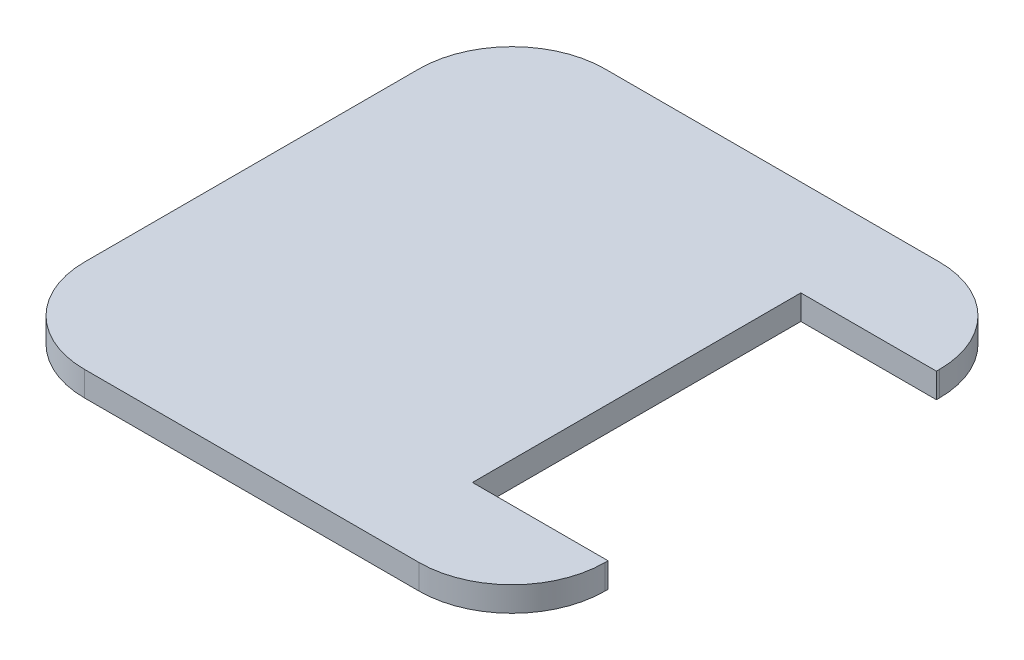
SolidWorks part; units mm, degrees
ref_plane "Front Plane" through (0, 0, 0) normal (0, 0, 1) x (1, 0, 0)
ref_plane "Top Plane" through (0, 0, 0) normal (0, 1, 0) x (1, 0, 0)
ref_plane "Right Plane" through (0, 0, 0) normal (1, 0, 0) x (0, 0, -1)
sketch "Layer1" plane through (0, 0, 0) normal (0, 1, 0) x (1, 0, 0)
  line L0 (11.25, 42) -> (27, 42)
  line L1 (-27, -42) -> (27, -42)
  line L2 (-42, -27) -> (-42, 27)
  line L3 (-27, 42) -> (27, 42)
  line L4 (42, -27) -> (42, 27)
  line L5 (-42, -42) -> (42, 42) construction
  line L6 (-42, 42) -> (42, -42) construction
  line L15 (11.25, -42) -> (27, -42)
  line L18 (-42, -21.5) -> (-42, 21.5)
  arc A0 (27, -42) -> (42, -27) centre (27, -27) ccw
  arc A1 (27, 42) -> (42, 27) centre (27, 27) cw
  arc A2 (-27, -42) -> (-42, -27) centre (-27, -27) cw
  arc A3 (-42, 27) -> (-27, 42) centre (-27, 27) cw
  point P0 (0, 0)
  point P27 (0, 0)
  point P30 (21.7219, 0)
  dimension "D9" = 15
  dimension "D1" = 84
  dimension "D2" = 84
  dimension "D10" = 43
extrude "Boss-Extrude1" add sketch "Layer1" along normal blind 4
sketch "Sketch4" plane through (0, 4, 0) normal (0, 1, 0) x (1, 0, 0)
  line L0 (-27, 42) -> (27, 42) construction
  line L1 (20.12, -26.5) -> (42, -26.5)
  line L2 (20.12, -26.5) -> (20.12, 26.5)
  line L3 (20.12, 26.5) -> (42, 26.5)
  line L4 (42, -26.5) -> (42, 26.5)
  line L5 (20.12, -26.5) -> (42, 26.5) construction
  line L6 (20.12, 26.5) -> (42, -26.5) construction
  line L7 (42, -27) -> (42, 27) construction
  line L8 (-42, -27) -> (-42, 27) construction
  line L13 (-27, 42) -> (27, 42) construction
  line L14 (-27, 42) -> (27, 42) construction
  line L19 (-20.9687, 38) -> (20.0313, 38)
  line L20 (-20.9687, 38) -> (-20.9687, -38)
  line L21 (-20.9687, -38) -> (20.0313, -38)
  line L22 (20.0313, 38) -> (20.0313, -38)
  line L23 (-20.9687, 38) -> (20.0313, -38) construction
  line L24 (-20.9687, -38) -> (20.0313, 38) construction
  line L25 (-27, -42) -> (27, -42) construction
  line L26 (-42, -13.1) -> (-15.8, -13.1)
  line L27 (-42, -13.1) -> (-42, 13.1)
  line L28 (-42, 13.1) -> (-15.8, 13.1)
  line L29 (-15.8, -13.1) -> (-15.8, 13.1)
  line L30 (-42, -13.1) -> (-15.8, 13.1) construction
  line L31 (-42, 13.1) -> (-15.8, -13.1) construction
  line L32 (-22.4151, 39.1322) -> (-22.4151, 27.3322)
  line L33 (-37.36, 26.5184) -> (-25.56, 26.5184)
  line L34 (-37.36, 26.5184) -> (-37.36, 14.7184)
  line L35 (-37.36, 14.7184) -> (-25.56, 14.7184)
  line L36 (-25.56, 26.5184) -> (-25.56, 14.7184)
  line L37 (-37.36, 26.5184) -> (-25.56, 14.7184) construction
  line L38 (-37.36, 14.7184) -> (-25.56, 26.5184) construction
  line L39 (-34.2151, 39.1322) -> (-34.2151, 27.3322)
  line L40 (-34.2151, 39.1322) -> (-22.4151, 39.1322)
  line L41 (-34.2151, 27.3322) -> (-22.4151, 27.3322)
  line L42 (-25.56, 26.5184) -> (-22.4151, 39.1322) construction
  line L43 (-37.36, -14.4816) -> (-25.56, -14.4816)
  line L44 (-37.36, -14.4816) -> (-37.36, -26.2816)
  line L45 (-37.36, -26.2816) -> (-25.56, -26.2816)
  line L46 (-25.56, -14.4816) -> (-25.56, -26.2816)
  line L47 (-34.2151, -38.6678) -> (-22.4151, -38.6678)
  line L48 (-22.4151, -26.8678) -> (-22.4151, -38.6678)
  line L49 (-34.2151, -26.8678) -> (-22.4151, -26.8678)
  line L50 (-34.2151, -26.8678) -> (-34.2151, -38.6678)
  circle A0 centre (-32, 32) radius 5
  circle A1 centre (32, 32) radius 5
  circle A2 centre (32, -32) radius 5
  circle A3 centre (-32, -32) radius 5
  point P0 (31.06, 0)
  point P9 (-0.4687, 0)
  point P28 (-28.9, 0)
  point P35 (-31.46, 20.6184)
  line M15 (42, -27) -> (42, 27)
  dimension "D9" = 10
  dimension "D1" = 53
  dimension "D2" = 21.88
  dimension "D3" = 15.5
  dimension "D4" = 0
  dimension "D10" = 10
  dimension "D11" = 10
  dimension "D5" = 76
  dimension "D6" = 41
  dimension "D7" = 4
  dimension "D8" = 26.2
  dimension "D14" = 0
  dimension "D15" = 28.9
  dimension "D16" = 11.8
  dimension "D18" = 13
  dimension "D12" = 2
  dimension "D13" = 2
  dimension "D17" = 2
  dimension "D19" = 2
  dimension "D20" = 2
extrude "Cut-Extrude1" cut sketch "Sketch4" against normal blind 4 contours L3 L2 L1 M15
equation "\"D2@Layer1\"=\"D1@Layer1\""
equation "\"D3@Sketch4\"=(\"D1@Layer1\"-\"D1@Sketch4\")/2"
equation "\"D11@Sketch4\"=\"D10@Sketch4\""
equation "\"D7@Sketch4\"=(\"D1@Layer1\"-\"D5@Sketch4\")/2"
equation "\"D15@Sketch4\"=(\"D1@Layer1\"-\"D8@Sketch4\")/2"
